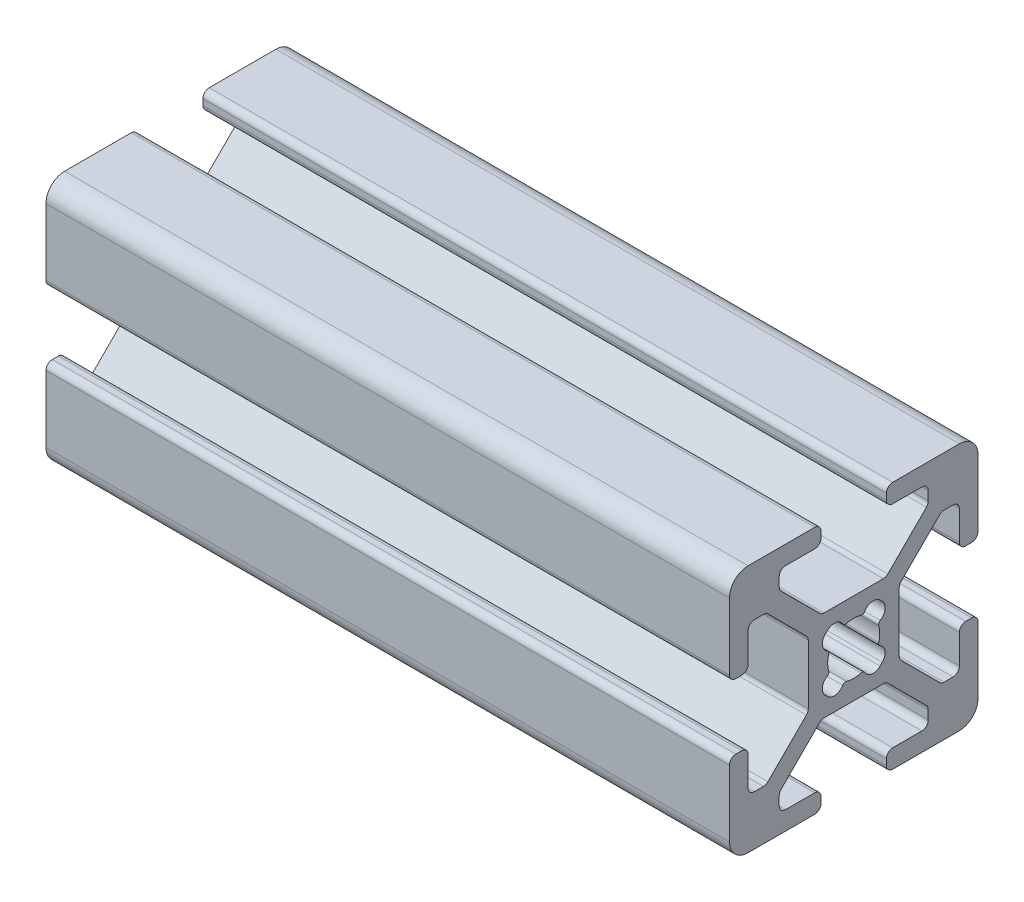
SolidWorks part; units mm, degrees
ref_plane "Front Plane" through (0, 0, 0) normal (0, 0, 1) x (1, 0, 0)
ref_plane "Top Plane" through (0, 0, 0) normal (0, 1, 0) x (1, 0, 0)
ref_plane "Right Plane" through (0, 0, 0) normal (1, 0, 0) x (0, 0, -1)
sketch "Sketch1" plane through (0, 0, 0) normal (0, 1, 0) x (1, 0, 0)
  line L0 (0, 0) -> (55, 0)
  dimension "D1" = 55
other "20_series 20-2020(1)"
ref_plane "Plane1" through (0, 0, 0) normal (1, 0, 0) x (0, 0, -1)
sketch "Sketch11" plane through (0, 0, 0) normal (1, 0, 0) x (0, 0, -1)
  line L0 (9.0094, 2.6289) -> (9.492, 2.6289)
  line L1 (8.5014, 5.4864) -> (8.5014, 3.1369)
  line L2 (10, 8.5014) -> (10, 3.1369)
  line L3 (7.2645, 5.9944) -> (7.9934, 5.9944)
  line L4 (3.1369, 10) -> (8.5014, 10)
  line L5 (3.8074, 2.7477) -> (6.9053, 5.8456)
  line L6 (2.6289, 9.0094) -> (2.6289, 9.492)
  line L7 (3.6586, -2.3885) -> (3.6586, 2.3885)
  line L8 (3.1369, 8.5014) -> (5.4864, 8.5014)
  line L9 (6.9053, -5.8456) -> (3.8074, -2.7477)
  line L10 (5.9944, 7.9934) -> (5.9944, 7.2645)
  line L11 (7.9934, -5.9944) -> (7.2645, -5.9944)
  line L12 (5.8456, 6.9053) -> (2.7477, 3.8074)
  line L13 (8.5014, -3.1369) -> (8.5014, -5.4864)
  line L14 (2.3885, 3.6586) -> (-2.3885, 3.6586)
  line L15 (9.0094, -2.6289) -> (9.492, -2.6289)
  line L16 (-2.7477, 3.8074) -> (-5.8456, 6.9053)
  line L17 (10, -3.1369) -> (10, -8.5014)
  line L18 (-5.9944, 7.2645) -> (-5.9944, 7.9934)
  line L19 (8.5014, -10) -> (3.1369, -10)
  line L20 (-5.4864, 8.5014) -> (-3.1369, 8.5014)
  line L21 (2.6289, -9.0094) -> (2.6289, -9.492)
  line L22 (-2.6289, 9.0094) -> (-2.6289, 9.492)
  line L23 (5.4864, -8.5014) -> (3.1369, -8.5014)
  line L24 (-8.5014, 10) -> (-3.1369, 10)
  line L25 (5.9944, -7.2645) -> (5.9944, -7.9934)
  line L26 (-10, 3.1369) -> (-10, 8.5014)
  line L27 (2.7477, -3.8074) -> (5.8456, -6.9053)
  line L28 (-9.0094, 2.6289) -> (-9.492, 2.6289)
  line L29 (-2.3885, -3.6586) -> (2.3885, -3.6586)
  line L30 (-8.5014, 3.1369) -> (-8.5014, 5.4864)
  line L31 (-5.8456, -6.9053) -> (-2.7477, -3.8074)
  line L32 (-7.9934, 5.9944) -> (-7.2645, 5.9944)
  line L33 (-5.9944, -7.9934) -> (-5.9944, -7.2645)
  line L34 (-6.9053, 5.8456) -> (-3.8074, 2.7477)
  line L35 (-3.1369, -8.5014) -> (-5.4864, -8.5014)
  line L36 (-3.6586, 2.3885) -> (-3.6586, -2.3885)
  line L37 (-2.6289, -9.0094) -> (-2.6289, -9.492)
  line L38 (-3.8074, -2.7477) -> (-6.9053, -5.8456)
  line L39 (-3.1369, -10) -> (-8.5014, -10)
  line L40 (-7.2645, -5.9944) -> (-7.9934, -5.9944)
  line L41 (-10, -8.5014) -> (-10, -3.1369)
  line L42 (-8.5014, -5.4864) -> (-8.5014, -3.1369)
  line L43 (-9.0094, -2.6289) -> (-9.492, -2.6289)
  line L44 (-2.2966, 2.1217) -> (-2.1217, 2.2966)
  line L45 (2.1217, 2.2966) -> (2.2966, 2.1217)
  line L46 (-2.1217, -2.2966) -> (-2.2966, -2.1217)
  line L47 (2.2966, -2.1217) -> (2.1217, -2.2966)
  arc A0 (8.5014, 3.1369) -> (9.0094, 2.6289) centre (9.0094, 3.1369) ccw
  arc A1 (9.492, 2.6289) -> (10, 3.1369) centre (9.492, 3.1369) ccw
  arc A2 (8.5014, 5.4864) -> (7.9934, 5.9944) centre (7.9934, 5.4864) ccw
  arc A3 (10, 8.5014) -> (8.5014, 10) centre (8.5014, 8.5014) ccw
  arc A4 (7.2645, 5.9944) -> (6.9053, 5.8456) centre (7.2645, 5.4864) ccw
  arc A5 (3.1369, 10) -> (2.6289, 9.492) centre (3.1369, 9.492) ccw
  arc A6 (3.8074, 2.7477) -> (3.6586, 2.3885) centre (4.1666, 2.3885) ccw
  arc A7 (2.6289, 9.0094) -> (3.1369, 8.5014) centre (3.1369, 9.0094) ccw
  arc A8 (3.6586, -2.3885) -> (3.8074, -2.7477) centre (4.1666, -2.3885) ccw
  arc A9 (5.9944, 7.9934) -> (5.4864, 8.5014) centre (5.4864, 7.9934) ccw
  arc A10 (6.9053, -5.8456) -> (7.2645, -5.9944) centre (7.2645, -5.4864) ccw
  arc A11 (5.8456, 6.9053) -> (5.9944, 7.2645) centre (5.4864, 7.2645) ccw
  arc A12 (7.9934, -5.9944) -> (8.5014, -5.4864) centre (7.9934, -5.4864) ccw
  arc A13 (2.3885, 3.6586) -> (2.7477, 3.8074) centre (2.3885, 4.1666) ccw
  arc A14 (9.0094, -2.6289) -> (8.5014, -3.1369) centre (9.0094, -3.1369) ccw
  arc A15 (-2.7477, 3.8074) -> (-2.3885, 3.6586) centre (-2.3885, 4.1666) ccw
  arc A16 (10, -3.1369) -> (9.492, -2.6289) centre (9.492, -3.1369) ccw
  arc A17 (-5.9944, 7.2645) -> (-5.8456, 6.9053) centre (-5.4864, 7.2645) ccw
  arc A18 (8.5014, -10) -> (10, -8.5014) centre (8.5014, -8.5014) ccw
  arc A19 (-5.4864, 8.5014) -> (-5.9944, 7.9934) centre (-5.4864, 7.9934) ccw
  arc A20 (2.6289, -9.492) -> (3.1369, -10) centre (3.1369, -9.492) ccw
  arc A21 (-3.1369, 8.5014) -> (-2.6289, 9.0094) centre (-3.1369, 9.0094) ccw
  arc A22 (3.1369, -8.5014) -> (2.6289, -9.0094) centre (3.1369, -9.0094) ccw
  arc A23 (-2.6289, 9.492) -> (-3.1369, 10) centre (-3.1369, 9.492) ccw
  arc A24 (5.4864, -8.5014) -> (5.9944, -7.9934) centre (5.4864, -7.9934) ccw
  arc A25 (-8.5014, 10) -> (-10, 8.5014) centre (-8.5014, 8.5014) ccw
  arc A26 (5.9944, -7.2645) -> (5.8456, -6.9053) centre (5.4864, -7.2645) ccw
  arc A27 (-10, 3.1369) -> (-9.492, 2.6289) centre (-9.492, 3.1369) ccw
  arc A28 (2.7477, -3.8074) -> (2.3885, -3.6586) centre (2.3885, -4.1666) ccw
  arc A29 (-9.0094, 2.6289) -> (-8.5014, 3.1369) centre (-9.0094, 3.1369) ccw
  arc A30 (-2.3885, -3.6586) -> (-2.7477, -3.8074) centre (-2.3885, -4.1666) ccw
  arc A31 (-7.9934, 5.9944) -> (-8.5014, 5.4864) centre (-7.9934, 5.4864) ccw
  arc A32 (-5.8456, -6.9053) -> (-5.9944, -7.2645) centre (-5.4864, -7.2645) ccw
  arc A33 (-6.9053, 5.8456) -> (-7.2645, 5.9944) centre (-7.2645, 5.4864) ccw
  arc A34 (-5.9944, -7.9934) -> (-5.4864, -8.5014) centre (-5.4864, -7.9934) ccw
  arc A35 (-3.6586, 2.3885) -> (-3.8074, 2.7477) centre (-4.1666, 2.3885) ccw
  arc A36 (-2.6289, -9.0094) -> (-3.1369, -8.5014) centre (-3.1369, -9.0094) ccw
  arc A37 (-3.8074, -2.7477) -> (-3.6586, -2.3885) centre (-4.1666, -2.3885) ccw
  arc A38 (-3.1369, -10) -> (-2.6289, -9.492) centre (-3.1369, -9.492) ccw
  arc A39 (-7.2645, -5.9944) -> (-6.9053, -5.8456) centre (-7.2645, -5.4864) ccw
  arc A40 (-10, -8.5014) -> (-8.5014, -10) centre (-8.5014, -8.5014) ccw
  arc A41 (-8.5014, -5.4864) -> (-7.9934, -5.9944) centre (-7.9934, -5.4864) ccw
  arc A42 (-9.492, -2.6289) -> (-10, -3.1369) centre (-9.492, -3.1369) ccw
  arc A43 (-8.5014, -3.1369) -> (-9.0094, -2.6289) centre (-9.0094, -3.1369) ccw
  arc A44 (-0.8806, 2.1293) -> (-0.5885, 2.0112) centre (-0.6599, 2.2549) ccw
  arc A45 (0.5885, 2.0112) -> (-0.5885, 2.0112) centre (0, 0) ccw
  arc A46 (-0.8806, 2.1293) -> (-2.1217, 2.2966) centre (-1.565, 1.7398) ccw
  arc A47 (0.5885, 2.0112) -> (0.8806, 2.1293) centre (0.6599, 2.2549) ccw
  arc A48 (2.1217, 2.2966) -> (0.8806, 2.1293) centre (1.565, 1.7398) ccw
  arc A49 (-2.2966, 2.1217) -> (-2.1293, 0.8806) centre (-1.7398, 1.565) ccw
  arc A50 (-2.0112, 0.5885) -> (-2.1293, 0.8806) centre (-2.2549, 0.6599) ccw
  arc A51 (2.1293, 0.8806) -> (2.2966, 2.1217) centre (1.7398, 1.565) ccw
  arc A52 (-2.0112, 0.5885) -> (-2.0112, -0.5885) centre (0, 0) ccw
  arc A53 (2.1293, 0.8806) -> (2.0112, 0.5885) centre (2.2549, 0.6599) ccw
  arc A54 (-2.1293, -0.8806) -> (-2.0112, -0.5885) centre (-2.2549, -0.6599) ccw
  arc A55 (2.0112, -0.5885) -> (2.0112, 0.5885) centre (0, 0) ccw
  arc A56 (-2.1293, -0.8806) -> (-2.2966, -2.1217) centre (-1.7398, -1.565) ccw
  arc A57 (2.0112, -0.5885) -> (2.1293, -0.8806) centre (2.2549, -0.6599) ccw
  arc A58 (2.2966, -2.1217) -> (2.1293, -0.8806) centre (1.7398, -1.565) ccw
  arc A59 (-2.1217, -2.2966) -> (-0.8806, -2.1293) centre (-1.565, -1.7398) ccw
  arc A60 (-0.5885, -2.0112) -> (-0.8806, -2.1293) centre (-0.6599, -2.2549) ccw
  arc A61 (0.8806, -2.1293) -> (2.1217, -2.2966) centre (1.565, -1.7398) ccw
  arc A62 (-0.5885, -2.0112) -> (0.5885, -2.0112) centre (0, 0) ccw
  arc A63 (0.8806, -2.1293) -> (0.5885, -2.0112) centre (0.6599, -2.2549) ccw
  point P0 (0, 0)
